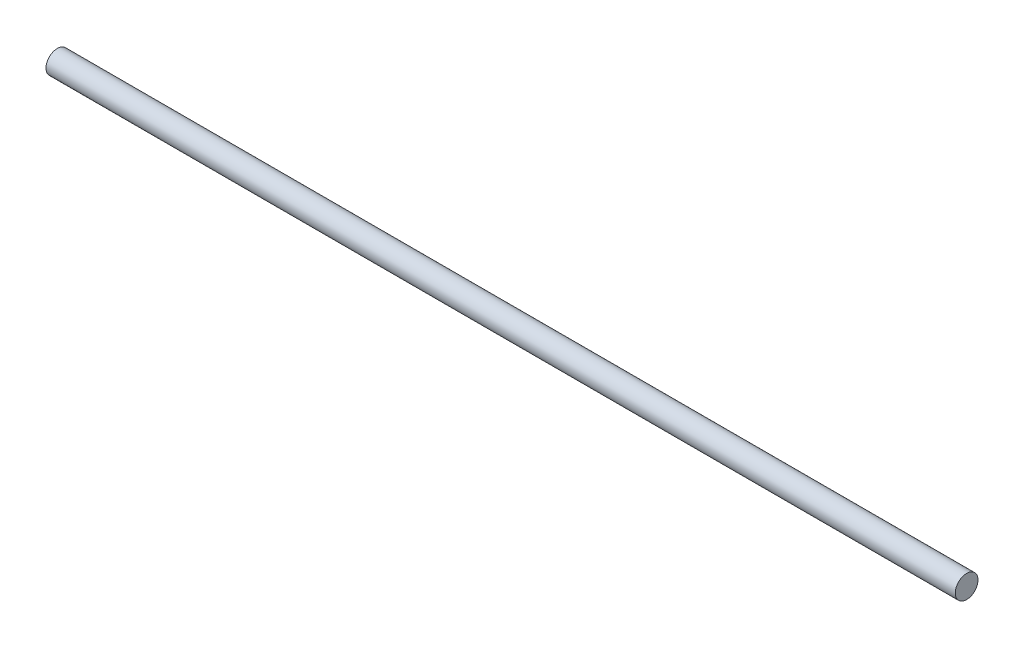
SolidWorks part; units mm, degrees
ref_plane "Front Plane" through (0, 0, 0) normal (0, 0, 1) x (1, 0, 0)
ref_plane "Top Plane" through (0, 0, 0) normal (0, 1, 0) x (1, 0, 0)
ref_plane "Right Plane" through (0, 0, 0) normal (1, 0, 0) x (0, 0, -1)
sketch "Sketch1" plane through (0, 0, 0) normal (1, 0, 0) x (0, 0, -1)
  circle A0 centre (0, 0) radius 1.25
extrude "Boss-Extrude1" add sketch "Sketch1" along normal blind 100
